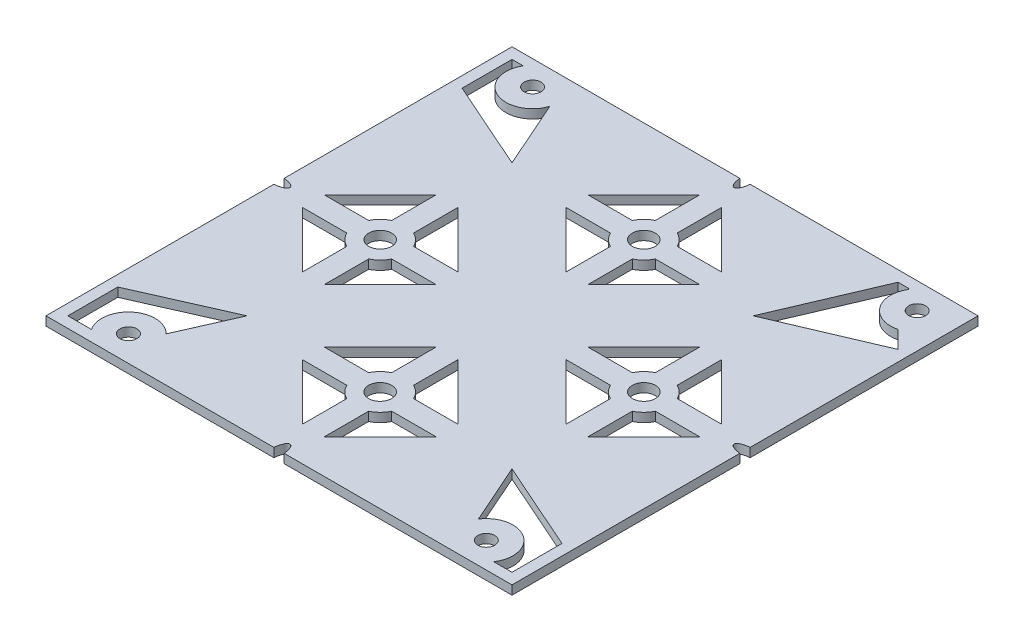
SolidWorks part; units mm, degrees
material "ABS"
ref_plane "Front Plane" through (0, 0, 0) normal (0, 0, 1) x (1, 0, 0)
ref_plane "Top Plane" through (0, 0, 0) normal (0, 1, 0) x (1, 0, 0)
ref_plane "Right Plane" through (0, 0, 0) normal (1, 0, 0) x (0, 0, -1)
sketch "Sketch1" plane through (0, 0, 0) normal (0, 1, 0) x (1, 0, 0)
  line L1 (0, 0) -> (97.6, 0)
  line L2 (0, 0) -> (0, 97.6)
  line L3 (0, 97.6) -> (97.6, 97.6)
  line L4 (97.6, 0) -> (97.6, 97.6)
  dimension "D1" = 97.6
  dimension "D2" = 97.6
extrude "Boss-Extrude1" add sketch "Sketch1" along normal blind 1.85
sketch "Sketch2" plane through (0, 0, 0) normal (0, -1, 0) x (-1, 0, 0)
  line L0 (-97.6, 97.6) -> (0, 0) construction
  line L1 (-97.6, 0) -> (0, 97.6) construction
  line L2 (-48.8, 97.6) -> (-48.8, 0) construction
  line L3 (-97.6, 97.6) -> (0, 97.6) construction
  line L4 (0, 0) -> (-97.6, 0) construction
  line L5 (-97.6, 48.8) -> (0, 48.8) construction
  line L6 (-97.6, 0) -> (-97.6, 97.6) construction
  line L7 (0, 97.6) -> (0, 0) construction
sketch "Sketch3" plane through (0, 0, 0) normal (0, -1, 0) x (1, 0, 0)
  line L0 (97.6, -97.6) -> (0, -97.6) construction
  line L1 (97.6, 0) -> (97.6, -97.6) construction
  line L2 (0, -97.6) -> (0, 0) construction
  line L3 (0, 0) -> (97.6, 0) construction
  line L4 (97.6, -94.6) -> (0, -94.6) construction
  line L5 (3, -97.6) -> (3, 0) construction
  line L6 (3, -94.6) -> (5.3161, -94.6)
  line L7 (3, -94.6) -> (3, -84.3)
  line L8 (3, -84.3) -> (21.4728, -76.1272)
  line L9 (97.6, 0) -> (0, -97.6) construction
  line L10 (21.4728, -76.1272) -> (13.3, -94.6)
  line L11 (21.4728, -21.4728) -> (13.3, -3)
  line L12 (3, -3) -> (13.3, -3)
  line L13 (0, -3) -> (97.6, -3) construction
  line L14 (3, -13.3) -> (3, -3)
  line L15 (3, -3) -> (7.8732, -3)
  line L16 (3, -13.3) -> (21.4728, -21.4728)
  line L17 (97.6, -97.6) -> (0, 0) construction
  line L18 (0, -97.6) -> (0, 0) construction
  line L19 (16.1614, -10.109) -> (21.4728, -21.4728) construction
  line L20 (94.6, -97.6) -> (94.6, 0) construction
  line L21 (94.6, -3) -> (94.6, -13.3)
  line L22 (94.6, -3) -> (84.3, -3)
  line L23 (94.6, -13.3) -> (76.1272, -21.4728)
  line L24 (76.1272, -21.4728) -> (84.3, -3)
  line L25 (94.6, -82.6) -> (73.6741, -73.6741)
  line L26 (73.6741, -73.6741) -> (82.6, -94.6)
  line L27 (94.6, -82.6) -> (82.6, -94.6) construction
  line L28 (94.6, -82.6) -> (91.0273, -86.1727)
  line L29 (82.6, -94.6) -> (85.1169, -94.6)
  line L30 (3, -94.6) -> (13.3, -94.6) construction
  circle A0 centre (89.66, -91.5) radius 1.25
  circle A1 centre (10.05, -91.8) radius 1.25
  circle A2 centre (12.45, -6.05) radius 1.25
  circle A3 centre (86.25, -6.05) radius 1.25
  circle A4 centre (89.66, -91.5) radius 5.5
  circle A5 centre (10.05, -91.8) radius 5.5
  circle A6 centre (12.45, -6.05) radius 5.5
  circle A7 centre (86.25, -6.05) radius 5.5
  dimension "D1" = 6.1
  dimension "D9" = 3
  dimension "D16" = 3
  dimension "D20" = 2.5
  dimension "D21" = 11
  dimension "D23" = 11
  dimension "D24" = 2.5
  dimension "D26" = 11
  dimension "D27" = 11
  dimension "D2" = 7.94
  dimension "D3" = 5.8
  dimension "D4" = 10.05
  dimension "D5" = 6.05
  dimension "D6" = 12.45
  dimension "D7" = 6.05
  dimension "D8" = 11.35
  dimension "D10" = 3
  dimension "D11" = 10.3
  dimension "D12" = 20.2
  dimension "D13" = 3
  dimension "D14" = 10.3
  dimension "D15" = 20.2
  dimension "D17" = 10.3
  dimension "D18" = 22.75
  dimension "D19" = 15
  dimension "D22" = 10.3
  dimension "D25" = 20.2
extrude "Cut-Extrude1" cut sketch "Sketch3" against normal blind 10
fillet "Fillet1" radius 0.2 1 edges at (85.1169, 0.925, -94.6)
sketch "Sketch5" plane through (0, 0, 0) normal (0, -1, 0) x (1, 0, 0)
  line L0 (78.0601, -69.3344) -> (24.4532, -15.7275) construction
  line L1 (15.9101, -24.6358) -> (67.2589, -75.9846) construction
  line L2 (97.6, -97.6) -> (0, 0) construction
  line L3 (25.594, -80.7317) -> (80.9701, -25.3556) construction
  line L4 (71.5743, -17.3) -> (16.8047, -72.0696) construction
  line L5 (97.6, 0) -> (0, -97.6) construction
  line L6 (51.05, -89.7671) -> (51.05, -80.6171)
  line L7 (46.55, -89.7671) -> (46.55, -80.6171)
  line L8 (48.8, -97.6) -> (48.8, 0) construction
  line L9 (51.05, -89.7671) -> (62.5825, -78.2346)
  line L10 (62.5825, -78.2346) -> (53.4325, -78.2346)
  line L11 (44.1675, -78.2346) -> (35.0175, -78.2346)
  line L12 (35.0175, -78.2346) -> (46.55, -89.7671)
  line L13 (48.8, -78.2346) -> (36.0473, -78.2346) construction
  line L14 (48.8, -73.7346) -> (36.0473, -73.7346) construction
  line L15 (44.1675, -73.7346) -> (35.0175, -73.7346)
  line L16 (46.55, -71.3521) -> (46.55, -62.2021)
  line L17 (53.4325, -73.7346) -> (62.5825, -73.7346)
  line L18 (51.05, -71.3521) -> (51.05, -62.2021)
  line L19 (62.5825, -73.7346) -> (51.05, -62.2021)
  line L20 (46.55, -62.2021) -> (35.0175, -73.7346)
  line L21 (48.8, -48.8) -> (-2.5605, -100.1605) construction
  line L22 (48.8, -48.8) -> (97.6, 0) construction
  line L23 (97.6, -97.6) -> (0, 0) construction
  line L24 (73.7346, -48.8) -> (73.7346, -36.0473) construction
  line L25 (78.2346, -48.8) -> (78.2346, -36.0473) construction
  line L26 (62.2021, -46.55) -> (73.7346, -35.0175)
  line L27 (73.7346, -62.5825) -> (62.2021, -51.05)
  line L28 (71.3521, -51.05) -> (62.2021, -51.05)
  line L29 (73.7346, -53.4325) -> (73.7346, -62.5825)
  line L30 (71.3521, -46.55) -> (62.2021, -46.55)
  line L31 (73.7346, -44.1675) -> (73.7346, -35.0175)
  line L32 (78.2346, -35.0175) -> (89.7671, -46.55)
  line L33 (78.2346, -44.1675) -> (78.2346, -35.0175)
  line L34 (78.2346, -62.5825) -> (78.2346, -53.4325)
  line L35 (89.7671, -51.05) -> (78.2346, -62.5825)
  line L36 (89.7671, -46.55) -> (80.6171, -46.55)
  line L37 (89.7671, -51.05) -> (80.6171, -51.05)
  line L38 (48.8, -19.3654) -> (61.5527, -19.3654) construction
  line L39 (48.8, -23.8654) -> (61.5527, -23.8654) construction
  line L40 (23.8654, -48.8) -> (23.8654, -61.5527) construction
  line L41 (19.3654, -48.8) -> (19.3654, -61.5527) construction
  line L42 (46.55, -7.8329) -> (46.55, -16.9829)
  line L43 (51.05, -7.8329) -> (51.05, -16.9829)
  line L44 (46.55, -7.8329) -> (35.0175, -19.3654)
  line L45 (35.0175, -19.3654) -> (44.1675, -19.3654)
  line L46 (53.4325, -19.3654) -> (62.5825, -19.3654)
  line L47 (62.5825, -19.3654) -> (51.05, -7.8329)
  line L48 (53.4325, -23.8654) -> (62.5825, -23.8654)
  line L49 (51.05, -26.2479) -> (51.05, -35.3979)
  line L50 (44.1675, -23.8654) -> (35.0175, -23.8654)
  line L51 (46.55, -26.2479) -> (46.55, -35.3979)
  line L52 (35.0175, -23.8654) -> (46.55, -35.3979)
  line L53 (51.05, -35.3979) -> (62.5825, -23.8654)
  line L54 (35.3979, -51.05) -> (23.8654, -62.5825)
  line L55 (23.8654, -35.0175) -> (35.3979, -46.55)
  line L56 (26.2479, -46.55) -> (35.3979, -46.55)
  line L57 (23.8654, -44.1675) -> (23.8654, -35.0175)
  line L58 (26.2479, -51.05) -> (35.3979, -51.05)
  line L59 (23.8654, -53.4325) -> (23.8654, -62.5825)
  line L60 (19.3654, -62.5825) -> (7.8329, -51.05)
  line L61 (19.3654, -53.4325) -> (19.3654, -62.5825)
  line L62 (19.3654, -35.0175) -> (19.3654, -44.1675)
  line L63 (7.8329, -46.55) -> (19.3654, -35.0175)
  line L64 (7.8329, -51.05) -> (16.9829, -51.05)
  line L65 (7.8329, -46.55) -> (16.9829, -46.55)
  line L66 (49.9, -97.6) -> (47.7, -97.6)
  line L67 (97.6, -97.6) -> (0, -97.6) construction
  line L68 (97.6, -48.8) -> (97.6, -49.9)
  line L69 (97.6, 0) -> (97.6, -97.6) construction
  line L70 (97.6, -48.8) -> (97.6, -47.7)
  line L71 (0, -49.9) -> (0, -48.8)
  line L72 (0, -97.6) -> (0, 0) construction
  line L73 (0, -48.8) -> (0, -47.7)
  line L74 (48.8, 0) -> (49.9, 0)
  line L75 (0, 0) -> (97.6, 0) construction
  line L76 (48.8, 0) -> (47.7, 0)
  circle A0 centre (48.8, -75.9846) radius 2.375
  circle A1 centre (48.8, -75.9846) radius 5.15
  circle A2 centre (75.9846, -48.8) radius 5.15
  circle A3 centre (75.9846, -48.8) radius 2.375
  circle A4 centre (48.8, -21.6154) radius 2.375
  circle A5 centre (48.8, -21.6154) radius 5.15
  circle A6 centre (21.6154, -48.8) radius 5.15
  circle A7 centre (21.6154, -48.8) radius 2.375
  ellipse E0 centre (48.8, -97.6) end of major axis (48.8, -94.6046) minor radius 1.1
  ellipse E1 centre (97.6, -48.8) end of major axis (94.5962, -48.8) minor radius 1.1
  ellipse E2 centre (0, -48.8) end of major axis (3, -48.8) minor radius 1.1
  ellipse E3 centre (48.8, 0) end of major axis (48.8, -3) minor radius 1.1
  line M15 (0, 0) -> (0, -97.6)
  line M16 (0, -97.6) -> (97.6, -97.6)
  line M17 (97.6, -97.6) -> (97.6, 0)
  line M18 (97.6, 0) -> (0, 0)
  dimension "D5" = 9.15
  dimension "D7" = 4.75
  dimension "D8" = 10.3
  dimension "D1" = 6.17
  dimension "D2" = 6.17
  dimension "D3" = 6.17
  dimension "D4" = 6.17
  dimension "D6" = 2.25
  dimension "D9" = 2.25
  dimension "D10" = 1.1
  dimension "D11" = 1.1
  dimension "D12" = 1.1
  dimension "D13" = 3
  dimension "D14" = 2.25
  dimension "D15" = 2.25
  dimension "D16" = 3
extrude "Cut-Extrude2" cut sketch "Sketch5" against normal blind 10 contours A1 L6 L9 L10 | A1 L11 L12 L7 | A0 | A1 L17 L19 L18 | A1 L16 L20 L15 | L61 A6 L64 L60 | L58 A6 L59 L54 | L57 A6 L56 L55 | L65 A6 L62 L63 | A7 | A3 | L37 A2 L34 L35 | L29 A2 L28 L27 | L30 A2 L31 L26 | L33 A2 L36 L32 | A5 L42 L44 L45 | A5 L46 L47 L43 | A5 L49 L53 L48 | A5 L50 L52 L51 | E0 M16 | E3 M18 | E1 M17 | E2 M15 | A4
sketch "Sketch6" plane through (0, 0, 0) normal (0, -1, 0) x (1, 0, 0)
  circle A0 centre (12.45, -6.05) radius 1.75
  circle A1 centre (86.25, -6.05) radius 1.75
  circle A2 centre (10.05, -91.8) radius 1.75
  circle A3 centre (89.66, -91.5) radius 1.75
  dimension "D1" = 3.5
  dimension "D2" = 3.5
  dimension "D3" = 3.5
  dimension "D4" = 3.5
extrude "Cut-Extrude3" cut sketch "Sketch6" against normal through all
sketch "Sketch7" plane through (0, 0, -97.6) normal (0, 0, -1) x (-1, 0, 0)
  line L1 (0, 0) -> (-97.6, 0)
  line L2 (0, 0) -> (0, 1.85)
  line L3 (0, 1.85) -> (-97.6, 1.85)
  line L4 (-97.6, 0) -> (-97.6, 1.85)
extrude "Cut-Extrude4" cut sketch "Sketch7" against normal blind 0.75
sketch "Sketch8" plane through (97.6, 0, 0) normal (1, 0, 0) x (0, 0, -1)
  line L1 (96.85, 0) -> (0, 0)
  line L2 (96.85, 0) -> (96.85, 1.85)
  line L3 (96.85, 1.85) -> (0, 1.85)
  line L4 (0, 0) -> (0, 1.85)
extrude "Cut-Extrude5" cut sketch "Sketch8" against normal blind 0.75
sketch "Sketch9" plane through (0, 0, 0) normal (0, 0, 1) x (1, 0, 0)
  line L1 (0, 0) -> (96.85, 0)
  line L2 (0, 0) -> (0, 1.85)
  line L3 (0, 1.85) -> (96.85, 1.85)
  line L4 (96.85, 0) -> (96.85, 1.85)
extrude "Cut-Extrude6" cut sketch "Sketch9" against normal blind 0.75
sketch "Sketch12" plane through (0, 0, 0) normal (-1, 0, 0) x (0, 0, 1)
  line L1 (-0.75, 0) -> (-96.85, 0)
  line L2 (-0.75, 0) -> (-0.75, 1.85)
  line L3 (-0.75, 1.85) -> (-96.85, 1.85)
  line L4 (-96.85, 0) -> (-96.85, 1.85)
extrude "Cut-Extrude7" cut sketch "Sketch12" against normal blind 0.75
